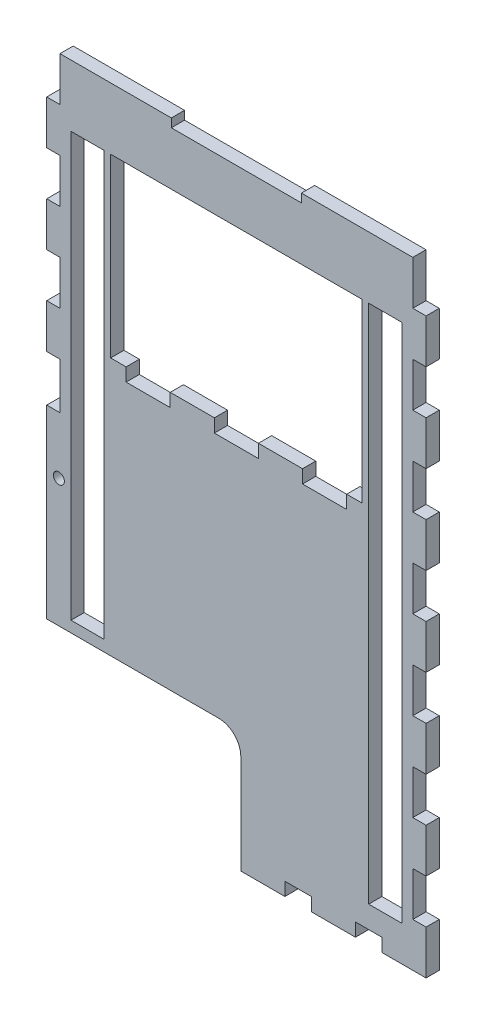
SolidWorks part; units mm, degrees
ref_plane "Front Plane" through (0, 0, 0) normal (0, 0, 1) x (1, 0, 0)
ref_plane "Top Plane" through (0, 0, 0) normal (0, 1, 0) x (1, 0, 0)
ref_plane "Right Plane" through (0, 0, 0) normal (1, 0, 0) x (0, 0, -1)
sketch "Sketch1" plane through (0, 0, 0) normal (0, 0, 1) x (1, 0, 0)
  line L0 (-86, 90.5) -> (-80, 90.5)
  line L1 (-80, 110.5) -> (80, 110.5)
  line L2 (-86, 90.5) -> (-86, 70.5)
  line L3 (-86, -169.5) -> (80, -169.5)
  line L4 (86, 90.5) -> (86, 70.5)
  line L5 (-86, 70.5) -> (-80, 70.5)
  line L6 (-80, 70.5) -> (-80, 50.5)
  line L7 (-80, 90.5) -> (-80, 110.5)
  line L8 (-153.1262, 0) -> (179.6732, 0) construction
  line L9 (0, 132.0302) -> (0, -136.811) construction
  line L10 (-80, 50.5) -> (-86, 50.5)
  line L11 (-86, 50.5) -> (-86, 30.5)
  line L12 (-86, 30.5) -> (-80, 30.5)
  line L13 (-80, 30.5) -> (-80, 10.5)
  line L14 (-80, 10.5) -> (-86, 10.5)
  line L15 (-86, -9.5) -> (-80, -9.5)
  line L16 (-80, -9.5) -> (-80, -30.5)
  line L17 (-80, -30.5) -> (-86, -30.5)
  line L18 (-86, 10.5) -> (-86, -9.5)
  line L19 (-86, -30.5) -> (-86, -169.5)
  line L20 (80, -29.5) -> (86, -29.5)
  line L21 (80, -9.5) -> (80, -29.5)
  line L22 (86, -9.5) -> (80, -9.5)
  line L23 (80, 10.5) -> (86, 10.5)
  line L24 (80, 30.5) -> (80, 10.5)
  line L25 (86, 50.5) -> (86, 30.5)
  line L26 (86, 30.5) -> (80, 30.5)
  line L27 (80, 50.5) -> (86, 50.5)
  line L28 (80, 70.5) -> (80, 50.5)
  line L29 (86, 70.5) -> (80, 70.5)
  line L30 (86, 90.5) -> (80, 90.5)
  line L31 (80, 90.5) -> (80, 110.5)
  line L32 (80, -109.5) -> (86, -109.5)
  line L33 (86, 10.5) -> (86, -9.5)
  line L34 (86, -29.5) -> (86, -49.5)
  line L35 (86, -49.5) -> (80, -49.5)
  line L36 (80, -49.5) -> (80, -69.5)
  line L37 (80, -69.5) -> (86, -69.5)
  line L38 (80, -89.5) -> (80, -109.5)
  line L39 (86, -69.5) -> (86, -89.5)
  line L40 (86, -89.5) -> (80, -89.5)
  line L41 (86, -109.5) -> (86, -129.5)
  line L42 (86, -129.5) -> (80, -129.5)
  line L43 (80, -149.5) -> (86, -149.5)
  line L44 (86, -149.5) -> (86, -169.5)
  line L45 (86, -169.5) -> (80, -169.5)
  line L46 (80, -129.5) -> (80, -149.5)
  point P0 (0, 0)
  dimension "D3" = 20
  dimension "D4" = 172
  dimension "D7" = 21
  dimension "D5" = 110.5
  dimension "D2" = 280
  dimension "D6" = 3
extrude "Boss-Extrude1" add sketch "Sketch1" along normal blind 6
sketch "Sketch2" plane through (0, 0, 0) normal (0, 0, 1) x (1, 0, 0)
  line L1 (-75, 82.5) -> (-60, 82.5)
  line L2 (-75, 82.5) -> (-75, -109.5)
  line L3 (-75, -109.5) -> (-60, -109.5)
  line L4 (-60, 82.5) -> (-60, -109.5)
  line L5 (0, 143.9028) -> (0, -122.652) construction
  line L6 (-86, -169.5) -> (80, -169.5) construction
  line L8 (60, 82.5) -> (75, 82.5)
  line L9 (60, 82.5) -> (60, -153.5)
  line L10 (60, -153.5) -> (75, -153.5)
  line L11 (-67.5, 82.5) -> (-67.5, -109.5) construction
  line L12 (75, 82.5) -> (75, -153.5)
  dimension "D1" = 60
  dimension "D2" = 15
  dimension "D4" = 192
  dimension "D3" = 60
  dimension "D5" = 60
  dimension "D6" = 236
extrude "Cut-Extrude1" cut sketch "Sketch2" along normal blind 6
sketch "Sketch3" plane through (0, 0, 6) normal (0, 0, 1) x (1, 0, 0)
  line L1 (-57, 82.5) -> (57, 82.5)
  line L2 (-57, 82.5) -> (-57, 2.5)
  line L3 (-57, 2.5) -> (57, 2.5)
  line L4 (57, 82.5) -> (57, 2.5)
  line L5 (0, 132.0302) -> (0, -136.811) construction
  line L7 (-60, 82.5) -> (-75, 82.5) construction
  point P6 (0, 82.5)
  dimension "D2" = 114
  dimension "D3" = 80
extrude "Cut-Extrude2" cut sketch "Sketch3" against normal blind 6
sketch "Sketch5" plane through (0, 0, 0) normal (0, 0, -1) x (-1, 0, 0)
  line L1 (57, 2.5) -> (-57, 2.5) construction
  line L2 (50, 2.5) -> (30, 2.5)
  line L3 (50, 2.5) -> (50, -3.5)
  line L4 (50, -3.5) -> (30, -3.5)
  line L5 (30, 2.5) -> (30, -3.5)
  line L6 (10, 2.5) -> (-10, 2.5)
  line L7 (10, 2.5) -> (10, -3.5)
  line L8 (10, -3.5) -> (-10, -3.5)
  line L9 (-10, 2.5) -> (-10, -3.5)
  line L10 (-30, 2.5) -> (-50, 2.5)
  line L11 (-30, 2.5) -> (-30, -3.5)
  line L12 (-30, -3.5) -> (-50, -3.5)
  line L13 (-50, 2.5) -> (-50, -3.5)
  line L16 (57, 82.5) -> (57, 2.5) construction
  dimension "D1" = 20
  dimension "D3" = 7
  dimension "D4" = 6
  dimension "D2" = 3
extrude "Cut-Extrude5" cut sketch "Sketch5" against normal blind 6
sketch "Sketch6" plane through (0, 0, 6) normal (0, 0, 1) x (1, 0, 0)
  line L2 (-86, -30.5) -> (-86, -169.5) construction
  line L3 (-86, -169.5) -> (80, -169.5) construction
  circle A0 centre (-80.5, -56.5) radius 2.5
  point P4 (-78, -56.8917)
  dimension "D3" = 5
  dimension "D1" = 5.5
  dimension "D2" = 113
extrude "Cut-Extrude7" cut sketch "Sketch6" against normal blind 6
sketch "Sketch7" plane through (0, 0, 0) normal (0, 0, -1) x (-1, 0, 0)
  line L0 (80, 110.5) -> (-80, 110.5) construction
  line L1 (-29.5, 110.5) -> (29.5, 110.5)
  line L2 (-29.5, 110.5) -> (-29.5, 106.63)
  line L3 (-29.5, 106.63) -> (29.5, 106.63)
  line L4 (29.5, 110.5) -> (29.5, 106.63)
  line L5 (0, 132.0302) -> (0, -136.811) construction
  point P8 (0, 110.5)
  dimension "D1" = 59
  dimension "D2" = 3.87
extrude "Cut-Extrude8" cut sketch "Sketch7" against normal blind 6
sketch "Sketch9" plane through (0, 0, 6) normal (0, 0, 1) x (1, 0, 0)
  line L1 (-86, -169.5) -> (2, -169.5)
  line L2 (-86, -169.5) -> (-86, -114.5)
  line L3 (-86, -114.5) -> (-8, -114.5)
  line L4 (2, -169.5) -> (2, -124.5)
  arc A0 (2, -124.5) -> (-8, -114.5) centre (-8, -124.5) ccw
  dimension "D3" = 10
  dimension "D1" = 88
  dimension "D2" = 55
extrude "Cut-Extrude10" cut sketch "Sketch9" against normal blind 6
sketch "Sketch10" plane through (0, 0, 6) normal (0, 0, 1) x (1, 0, 0)
  line L0 (2, -169.5) -> (86, -169.5) construction
  line L1 (22, -169.5) -> (34, -169.5)
  line L2 (22, -169.5) -> (22, -163.5)
  line L3 (22, -163.5) -> (34, -163.5)
  line L4 (34, -169.5) -> (34, -163.5)
  line L6 (54, -163.5) -> (66, -163.5)
  line L7 (54, -163.5) -> (54, -169.5)
  line L8 (54, -169.5) -> (66, -169.5)
  line L9 (66, -163.5) -> (66, -169.5)
  dimension "D1" = 12
  dimension "D2" = 20
  dimension "D4" = 20
extrude "Cut-Extrude11" cut sketch "Sketch10" against normal blind 6
equation "\"Material Thickness\"= 6mm"
equation "\"D1@Sketch1\"=\"Material Thickness\""
equation "\"D1@Boss-Extrude1\"=\"Material Thickness\""
equation "\"D4@Sketch2\"=\"D2@Sketch1\" - \"D3@Sketch2\" -28"
equation "\"D1@Cut-Extrude1\"=\"Material Thickness\""
equation "\"D1@Cut-Extrude2\"=\"Material Thickness\""
equation "\"D1@Cut-Extrude5\"=\"Material Thickness\""
equation "\"D1@Cut-Extrude7\" = \"Material Thickness\""
equation "\"D2@Sketch7\"=\"Material Thickness\"-2.13"
equation "\"D1@Cut-Extrude8\"=\"Material Thickness\""
equation "\"D4@Sketch1\"=(2*\"Material Thickness\")+160"
equation "\"D1@Sketch2\"=(\"D4@Sketch1\"/2) - 20-\"Material Thickness\""
equation "\"D5@Sketch2\"=\"D1@Sketch2\""
equation "\"D6@Sketch2\"=\"D4@Sketch2\"+\"D3@Sketch2\"-\"Material Thickness\"-10"
equation "\"D2@Sketch3\"=(2*\"D1@Sketch2\")-6"
equation "\"D1@Sketch5\"=20"
equation "\"D3@Sketch5\"=(\"D2@Sketch3\"-(5*\"D1@Sketch5\"))/2"
equation "\"D4@Sketch5\"=\"Material Thickness\""
equation "\"D1@Sketch6\"=(\"Material Thickness\"+5)/2"
equation "\"D1@Cut-Extrude10\"=\"Material Thickness\""
equation "\"D3@Sketch10\"=\"Material Thickness\""
equation "\"D1@Cut-Extrude11\"=\"Material Thickness\""
equation "\"D4@Sketch10\"=\"D2@Sketch10\""
